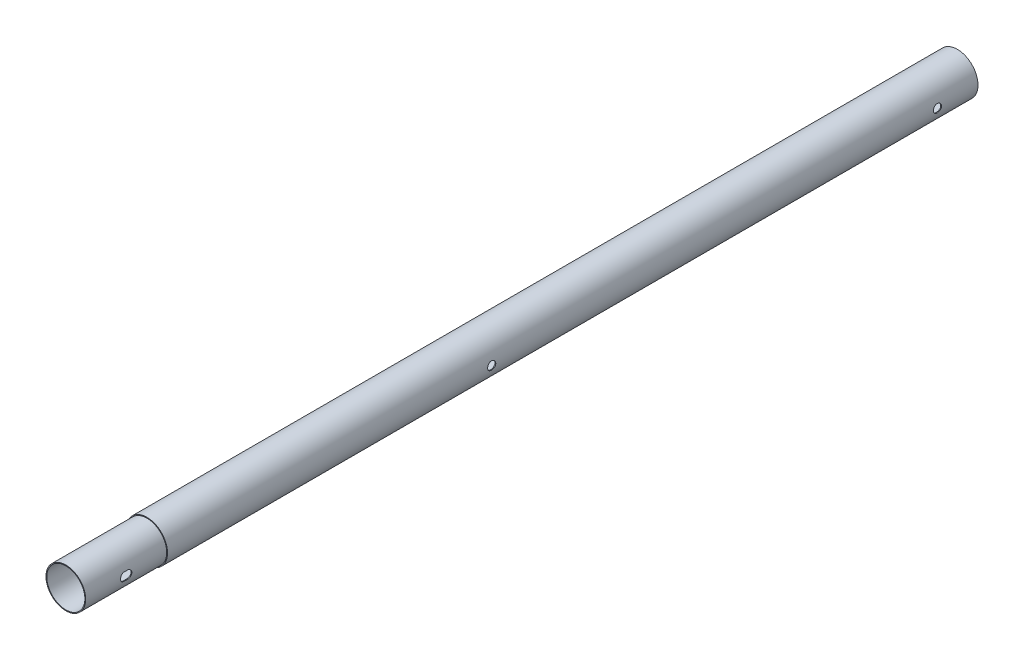
SolidWorks part; units mm, degrees
ref_plane "Płaszczyzna przednia" through (0, 0, 0) normal (0, 0, 1) x (1, 0, 0)
ref_plane "Płaszczyzna górna" through (0, 0, 0) normal (0, 1, 0) x (1, 0, 0)
ref_plane "Płaszczyzna prawa" through (0, 0, 0) normal (1, 0, 0) x (0, 0, -1)
sketch "Szkic1" plane through (0, 0, 0) normal (0, 0, 1) x (1, 0, 0)
  circle A0 centre (0, 0) radius 25.5
  circle A1 centre (0, 0) radius 24.5
  dimension "D1" = 51
  dimension "D2" = 49
extrude "Dodanie-wyciągnięcie1" add sketch "Szkic1" along normal blind 1000
sketch "Szkic3" plane through (0, 0, 1000) normal (0, 0, 1) x (1, 0, 0)
  circle A0 centre (0, 0) radius 24.5
  circle A1 centre (0, 0) radius 23.5
  dimension "D1" = 49
  dimension "D2" = 47
extrude "Dodanie-wyciągnięcie2" add sketch "Szkic3" along normal blind 100 contours A0
hole_wizard "Otwory ustalające Ø10.0mm1" positions "Szkic 3D1" profile "Szkic9" hole size "Ø10.0" standard "BSI" end condition through all
sketch3d "Szkic 3D1"
  point P0 (25.5, 0, 50)
sketch "Szkic9" plane through (25.5, 0, 50) normal (0, 1, 0) x (0, 0, -1)
  line L0 (0, 0) -> (0, 51)
  line L1 (0, 51) -> (5, 51)
  line L2 (5, 51) -> (5, 0.025)
  line L3 (5, 0.025) -> (5.025, 0)
  line L5 (5.025, 0) -> (0, 0)
  line L6 (-5, 0.025) -> (-5.025, 0) construction
  line L11 (0, -6.35) -> (0, 107.95) construction
  dimension "Średnica otworu na wylot" = 10
  dimension "Głębokość otworu na wylot" = 51
  dimension "Średnica zewnętrznego pogłębienia stożkowego" = 10.05
  dimension "Kąt zewnętrznego pogłębienia stożkowego" = 90
hole_wizard "Otwory ustalające Ø10.0mm2" positions "Szkic 3D2" profile "Szkic10" hole size "Ø10.0" standard "BSI" end condition through all
sketch3d "Szkic 3D2"
  point P0 (24.5, 0, 1052)
  point P2 (24.5, 0, 1048)
sketch "Szkic10" plane through (24.5, 0, 1052) normal (0, 1, 0) x (0, 0, -1)
  line L0 (0, 0) -> (0, 50)
  line L1 (0, 50) -> (5, 50)
  line L2 (5, 50) -> (5, 0.025)
  line L3 (5, 0.025) -> (5.025, 0)
  line L5 (5.025, 0) -> (0, 0)
  line L6 (-5, 0.025) -> (-5.025, 0) construction
  line L11 (0, -6.35) -> (0, 107.95) construction
  dimension "Średnica otworu na wylot" = 10
  dimension "Głębokość otworu na wylot" = 50
  dimension "Średnica zewnętrznego pogłębienia stożkowego" = 10.05
  dimension "Kąt zewnętrznego pogłębienia stożkowego" = 90
hole_wizard "Otwory ustalające Ø10.0mm4" positions "Szkic 3D4" profile "Szkic12" hole size "Ø10.0" standard "BSI" end condition through all
sketch3d "Szkic 3D4"
  point P0 (24.5, 0, 1050)
sketch "Szkic12" plane through (24.5, 0, 1050) normal (0, 1, 0) x (0, 0, -1)
  line L0 (0, 0) -> (0, 50)
  line L1 (0, 50) -> (5, 50)
  line L2 (5, 50) -> (5, 0.025)
  line L3 (5, 0.025) -> (5.025, 0)
  line L5 (5.025, 0) -> (0, 0)
  line L6 (-5, 0.025) -> (-5.025, 0) construction
  line L11 (0, -6.35) -> (0, 107.95) construction
  dimension "Średnica otworu na wylot" = 10
  dimension "Głębokość otworu na wylot" = 50
  dimension "Średnica zewnętrznego pogłębienia stożkowego" = 10.05
  dimension "Kąt zewnętrznego pogłębienia stożkowego" = 90
hole_wizard "Otwory ustalające Ø10.0mm5" positions "Szkic 3D5" profile "Szkic13" hole size "Ø10.0" standard "BSI" end condition through all
sketch3d "Szkic 3D5"
  point P0 (24.5, 0, 1051)
sketch "Szkic13" plane through (24.5, 0, 1051) normal (0, 1, 0) x (0, 0, -1)
  line L0 (0, 0) -> (0, 50)
  line L1 (0, 50) -> (5, 50)
  line L2 (5, 50) -> (5, 0.025)
  line L3 (5, 0.025) -> (5.025, 0)
  line L5 (5.025, 0) -> (0, 0)
  line L6 (-5, 0.025) -> (-5.025, 0) construction
  line L11 (0, -6.35) -> (0, 107.95) construction
  dimension "Średnica otworu na wylot" = 10
  dimension "Głębokość otworu na wylot" = 50
  dimension "Średnica zewnętrznego pogłębienia stożkowego" = 10.05
  dimension "Kąt zewnętrznego pogłębienia stożkowego" = 90
hole_wizard "Otwory ustalające Ø10.0mm6" positions "Szkic 3D6" profile "Szkic14" hole size "Ø10.0" standard "BSI" end condition through all
sketch3d "Szkic 3D6"
  point P0 (24.5, 0, 1049)
sketch "Szkic14" plane through (24.5, 0, 1049) normal (0, 1, 0) x (0, 0, -1)
  line L0 (0, 0) -> (0, 50)
  line L1 (0, 50) -> (5, 50)
  line L2 (5, 50) -> (5, 0.025)
  line L3 (5, 0.025) -> (5.025, 0)
  line L5 (5.025, 0) -> (0, 0)
  line L6 (-5, 0.025) -> (-5.025, 0) construction
  line L11 (0, -6.35) -> (0, 107.95) construction
  dimension "Średnica otworu na wylot" = 10
  dimension "Głębokość otworu na wylot" = 50
  dimension "Średnica zewnętrznego pogłębienia stożkowego" = 10.05
  dimension "Kąt zewnętrznego pogłębienia stożkowego" = 90
hole_wizard "Otwory ustalające Ø10.0mm7" positions "Szkic 3D7" profile "Szkic15" hole size "Ø10.0" standard "BSI" end condition through all
sketch3d "Szkic 3D7"
  point P0 (25.5, 0, 600)
sketch "Szkic15" plane through (25.5, 0, 600) normal (0, 1, 0) x (0, 0, -1)
  line L0 (0, 0) -> (0, 51)
  line L1 (0, 51) -> (5, 51)
  line L2 (5, 51) -> (5, 0.025)
  line L3 (5, 0.025) -> (5.025, 0)
  line L5 (5.025, 0) -> (0, 0)
  line L6 (-5, 0.025) -> (-5.025, 0) construction
  line L11 (0, -6.35) -> (0, 107.95) construction
  dimension "Średnica otworu na wylot" = 10
  dimension "Głębokość otworu na wylot" = 51
  dimension "Średnica zewnętrznego pogłębienia stożkowego" = 10.05
  dimension "Kąt zewnętrznego pogłębienia stożkowego" = 90
sketch "Szkic16" plane through (0, 0, 1100) normal (0, 0, 1) x (1, 0, 0)
  circle A0 centre (0, 0) radius 23.5
  dimension "D1" = 47
extrude "Wytnij-wyciągnięcie1" cut sketch "Szkic16" against normal through all
